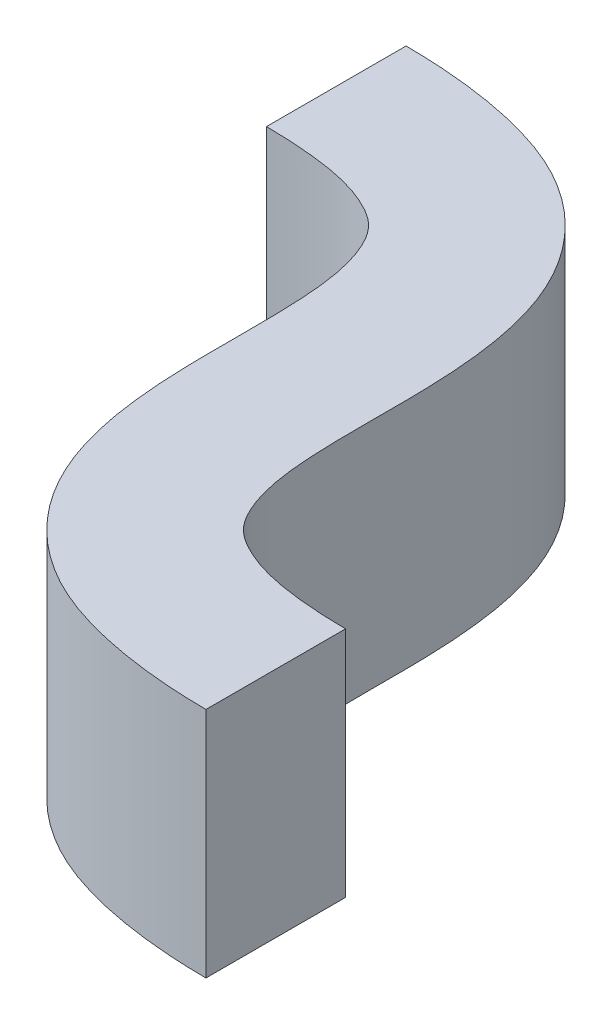
SolidWorks part; units mm, degrees
ref_plane "Front Plane" through (0, 0, 0) normal (0, 0, 1) x (1, 0, 0)
ref_plane "Top Plane" through (0, 0, 0) normal (0, 1, 0) x (1, 0, 0)
ref_plane "Right Plane" through (0, 0, 0) normal (1, 0, 0) x (0, 0, -1)
sketch "Sketch1" plane through (0, 0, 0) normal (0, 1, 0) x (1, 0, 0)
  line L0 (0, 0) -> (1.02, 0) construction
  line L1 (1.02, 0) -> (0, -1.15) construction
  line L2 (0, -1.15) -> (1.02, -1.15) construction
  line L3 (0, -0.15) -> (0, 0.15)
  line L4 (1.02, -1.3) -> (1.02, -1)
  spline S0 degree 3 poles (0, 0) (1.02, 0) (0, -1.15) (1.02, -1.15) knots 0 0 0 0 1 1 1 1 construction
  spline S1 degree 1 poles (0, -0.15) (1.02, -1.3) knots 0 0 1 1 construction
  spline S2 degree 3 poles (0, -0.15) (0.0477, -0.15) (0.1557, -0.1579) (0.2688, -0.1963) (0.3213, -0.2454) (0.3591, -0.3682) (0.3605, -0.5706) (0.3587, -0.7994) (0.4186, -1.0542) (0.6346, -1.2639) (0.8998, -1.3) (1.02, -1.3) knots 0 0 0 0 0.0625 0.125 0.25 0.375 0.5 0.625 0.75 0.875 1 1 1 1
  spline S3 degree 1 poles (0, 0.15) (1.02, -1) knots 0 0 1 1 construction
  spline S4 degree 3 poles (0, 0.15) (0.1202, 0.15) (0.3854, 0.1139) (0.6014, -0.0958) (0.6613, -0.3506) (0.6595, -0.5794) (0.6609, -0.7818) (0.6987, -0.9046) (0.7512, -0.9537) (0.8643, -0.9921) (0.9723, -1) (1.02, -1) knots 0 0 0 0 0.125 0.25 0.375 0.5 0.625 0.75 0.875 0.9375 1 1 1 1
  point P4 (0.5643, -1.1316)
  point P6 (0.2018, -1.15)
  point P7 (0, 0)
  dimension "D1" = 1.15
  dimension "D2" = 1.02
  dimension "D3" = 0.15
  dimension "D4" = 0.15
extrude "Boss-Extrude1" add sketch "Sketch1" along normal mid plane 0.5
